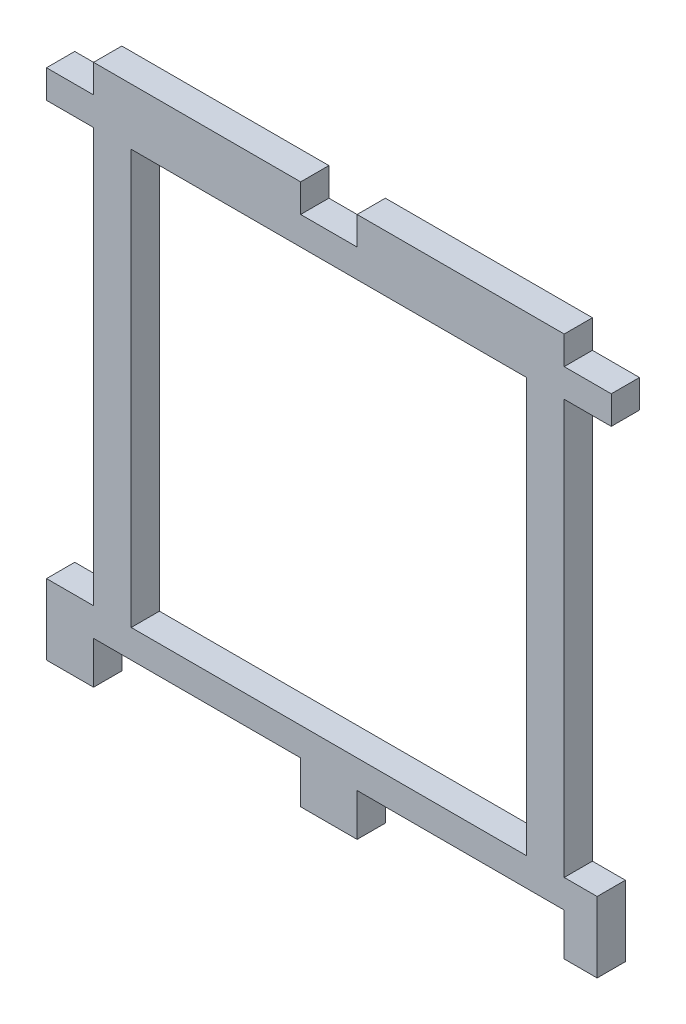
SolidWorks part; units mm, degrees
material "Custom Plastic"
ref_plane "Front Plane" through (0, 0, 0) normal (0, 0, 1) x (1, 0, 0)
ref_plane "Top Plane" through (0, 0, 0) normal (0, 1, 0) x (1, 0, 0)
ref_plane "Right Plane" through (0, 0, 0) normal (1, 0, 0) x (0, 0, -1)
sketch "Sketch1" plane through (0, 0, 0) normal (0, 0, 1) x (1, 0, 0)
  line L46 (0, 0) -> (5, 0)
  line L47 (5, 0) -> (5, 3)
  line L48 (5, 3) -> (27, 3)
  line L49 (27, 3) -> (27, 0)
  line L50 (27, 0) -> (33, 0)
  line L51 (33, 0) -> (33, 3)
  line L52 (33, 3) -> (55, 3)
  line L53 (55, 3) -> (55, 0)
  line L54 (55, 0) -> (60, 0)
  line L55 (60, 0) -> (60, -3)
  line L56 (60, -3) -> (55, -3)
  line L57 (55, -3) -> (55, -47)
  line L58 (55, -47) -> (58.5, -47)
  line L59 (58.5, -47) -> (58.5, -54.5)
  line L60 (58.5, -54.5) -> (55, -54.5)
  line L61 (55, -54.5) -> (55, -50)
  line L62 (55, -50) -> (33, -50)
  line L63 (33, -50) -> (33, -54.5)
  line L64 (33, -54.5) -> (27, -54.5)
  line L65 (27, -54.5) -> (27, -50)
  line L66 (27, -50) -> (5, -50)
  line L67 (5, -50) -> (5, -54.5)
  line L68 (5, -54.5) -> (0, -54.5)
  line L69 (0, -54.5) -> (0, -47)
  line L70 (0, -47) -> (5, -47)
  line L71 (0, 0) -> (0, -3)
  line L72 (0, -3) -> (5, -3)
  line L73 (5, -3) -> (5, -47)
  line L74 (9, -3) -> (9, -47)
  line L75 (9, -47) -> (51, -47)
  line L76 (51, -47) -> (51, -3)
  line L77 (51, -3) -> (9, -3)
  dimension "D10" = 5
  dimension "D11" = 3
  dimension "D12" = 22
  dimension "D13" = 6
  dimension "D14" = 22
  dimension "D15" = 5
  dimension "D16" = 3
  dimension "D17" = 44
  dimension "D18" = 7.5
  dimension "D19" = 3.5
  dimension "D20" = 3
  dimension "D21" = 22
  dimension "D22" = 6
  dimension "D23" = 4
  dimension "D24" = 4
extrude "Boss-Extrude1" add sketch "Sketch1" along normal blind 3
